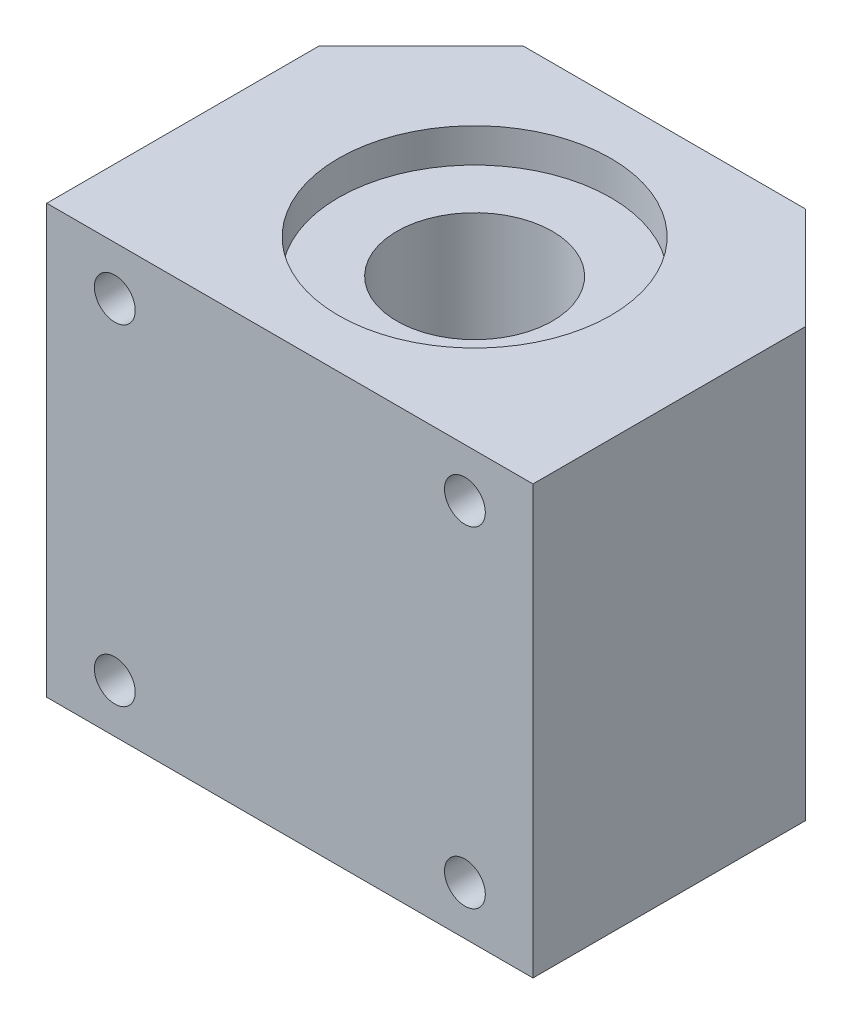
SolidWorks part; units mm, degrees
ref_plane "Front Plane" through (0, 0, 0) normal (0, 0, 1) x (1, 0, 0)
ref_plane "Top Plane" through (0, 0, 0) normal (0, 1, 0) x (1, 0, 0)
ref_plane "Right Plane" through (0, 0, 0) normal (1, 0, 0) x (0, 0, -1)
sketch "Sketch1" plane through (0, 0, 0) normal (0, 0, 1) x (1, 0, 0)
  line L1 (-25, 22) -> (25, 22)
  line L2 (-25, 22) -> (-25, -22)
  line L3 (-25, -22) -> (25, -22)
  line L4 (25, 22) -> (25, -22)
  line L5 (-25, 22) -> (25, -22) construction
  line L6 (-25, -22) -> (25, 22) construction
  dimension "D1" = 44
  dimension "D2" = 50
extrude "Boss-Extrude1" add sketch "Sketch1" along normal blind 38.5
hole_wizard "M5 Tapped Hole1" positions "Sketch4" profile "Sketch5" tap size "M5" standard "ISO" end condition through all
sketch "Sketch4" plane through (0, 0, 38.5) normal (0, 0, 1) x (1, 0, 0)
  line L0 (-25, 0) -> (25, 0) construction
  line L1 (-25, 22) -> (-25, -22) construction
  line L2 (25, -22) -> (25, 22) construction
  line L4 (25, 22) -> (-25, 22) construction
  line L5 (0, 22) -> (0, -22) construction
  line L6 (-25, -22) -> (25, -22) construction
  point P0 (-18, 17)
  point P2 (18, 17)
  point P4 (18, -17)
  point P6 (-18, -17)
  dimension "D1" = 36
  dimension "D2" = 34
sketch "Sketch5" plane through (-18, 17, 38.5) normal (1, 0, 0) x (0, -1, 0)
  line L0 (0, 0) -> (0, 38.5)
  line L1 (0, 38.5) -> (2.1, 38.5)
  line L2 (2.1, 38.5) -> (2.1, 0)
  line L5 (2.1, 0) -> (0, 0)
  line L11 (0, -6.35) -> (0, 107.95) construction
  dimension "Thru Tap Drill Dia." = 4.2
  dimension "Thru Tap Drill Depth" = 38.5
cosmetic thread "Hole Thread1" parameters "D2"=5
cosmetic thread "Hole Thread2" parameters "D2"=5
cosmetic thread "Hole Thread3" parameters "D2"=5
cosmetic thread "Hole Thread4" parameters "D2"=5
sketch "Sketch6" plane through (0, 22, 0) normal (0, 1, 0) x (1, 0, 0)
  line L0 (-25, -10.5) -> (-14.5, 0)
  line L1 (-25, -38.5) -> (-25, 0) construction
  line L2 (25, 0) -> (-25, 0) construction
  line L3 (-25, -10.5) -> (-25, 0)
  line L4 (-25, 0) -> (-14.5, 0)
  line L5 (0, 0) -> (0, -38.5) construction
  line L6 (25, -38.5) -> (-25, -38.5) construction
  line L7 (25, -10.5) -> (14.5, 0)
  line L8 (25, 0) -> (14.5, 0)
  line L9 (25, -10.5) -> (25, 0)
  circle A0 centre (0, -19.5) radius 14
  dimension "D3" = 28
  dimension "D4" = 19
  dimension "D1" = 45
  dimension "D2" = 10.5
extrude "Cut-Extrude1" cut sketch "Sketch6" against normal through all
ref_plane "Plane1" through (0, 0, 0) normal (0, -1, 0) x (-1, 0, 0)
sketch "Sketch8" plane through (0, 0, 0) normal (0, -1, 0) x (-1, 0, 0)
  circle A0 centre (0, -19.5) radius 8
  circle A1 centre (0, -19.5) radius 14 construction
  circle A2 centre (0, -19.5) radius 14
  dimension "D1" = 16
  dimension "D2" = 28
extrude "Boss-Extrude2" add sketch "Sketch8" along normal mid plane 37
